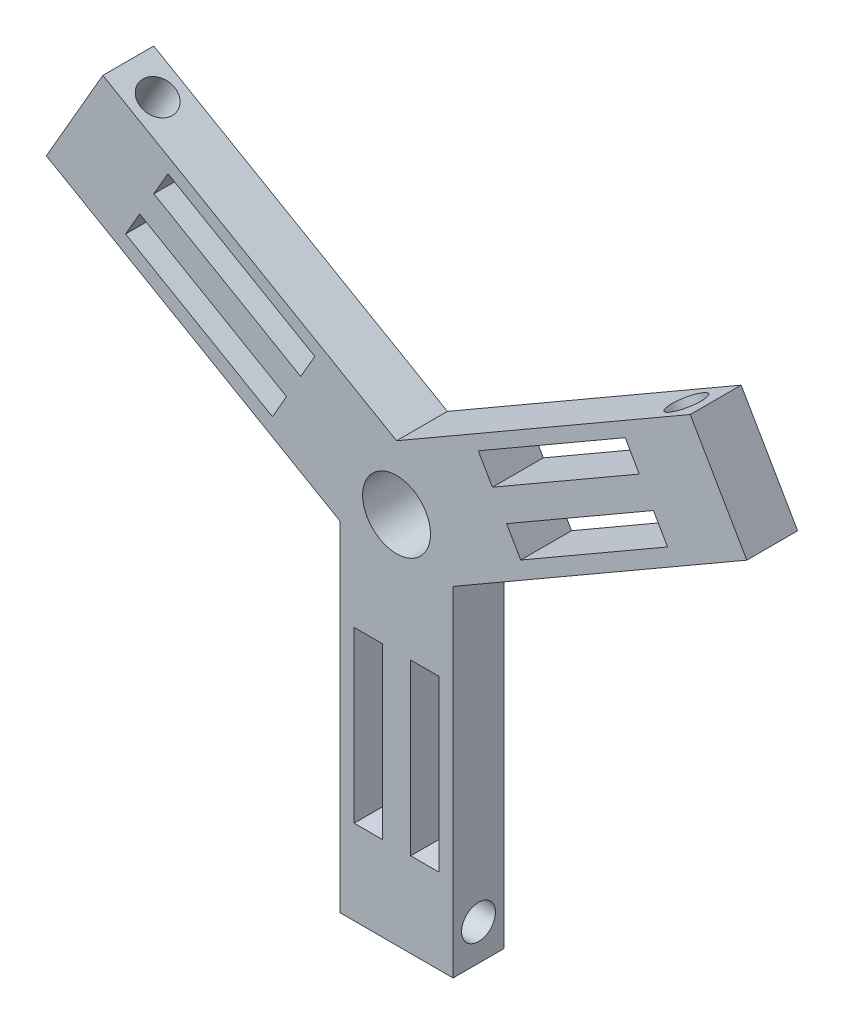
SolidWorks part; units mm, degrees
ref_plane "Front Plane" through (0, 0, 0) normal (0, 0, 1) x (1, 0, 0)
ref_plane "Top Plane" through (0, 0, 0) normal (0, 1, 0) x (1, 0, 0)
ref_plane "Right Plane" through (0, 0, 0) normal (1, 0, 0) x (0, 0, -1)
sketch "Sketch2" plane through (0, 0, 0) normal (0, 0, 1) x (1, 0, 0)
  line L4 (-100, -60) -> (-100, -660)
  line L5 (-100, -660) -> (100, -660)
  line L6 (100, -660) -> (100, -60)
  line L7 (0, 113.2051) -> (519.6152, 413.2051)
  line L8 (519.6152, 413.2051) -> (619.6152, 240)
  line L9 (619.6152, 240) -> (100, -60)
  line L10 (0, 113.2051) -> (-519.6152, 413.2051)
  line L11 (-519.6152, 413.2051) -> (-619.6152, 240)
  line L12 (-619.6152, 240) -> (-100, -60)
  circle A0 centre (0, 0) radius 60
  point P10 (0, 0)
  dimension "D1" = 120
  dimension "D2" = 200
  dimension "D3" = 200
  dimension "D4" = 600
  dimension "D5" = 200
  dimension "D6" = 600
  dimension "D7" = 600
  dimension "D8" = 200
  dimension "D9" = 660
extrude "Boss-Extrude1" add sketch "Sketch2" along normal blind 90
sketch "Sketch4" plane through (0, 0, 90) normal (0, 0, 1) x (1, 0, 0)
  line L0 (0, 0) -> (0, -738.4835) construction
  line L1 (50, -360.3099) -> (50, -363.0394) construction
  line L2 (-25, -510.3099) -> (-75, -510.3099)
  line L3 (49.5451, -363.0394) -> (50.4549, -363.0394) construction
  line L4 (25, -210.3099) -> (75, -210.3099)
  line L5 (25, -210.3099) -> (25, -510.3099)
  line L6 (25, -510.3099) -> (75, -510.3099)
  line L7 (75, -210.3099) -> (75, -510.3099)
  line L8 (25, -210.3099) -> (75, -510.3099) construction
  line L9 (25, -510.3099) -> (75, -210.3099) construction
  line L10 (-75, -210.3099) -> (-75, -510.3099)
  line L11 (-25, -210.3099) -> (-75, -210.3099)
  line L12 (-25, -210.3099) -> (-25, -510.3099)
  point P5 (0, -591.5751)
  point P6 (0, -738.4835)
  point P8 (50, -360.3099)
  dimension "D2" = 300
  dimension "D3" = 50
extrude "Cut-Extrude1" cut sketch "Sketch4" against normal blind 90
pattern_circular "CirPattern1" count 3 every 120 about axis through (0, 0, 0) along (0, 0, 1) of "Cut-Extrude1"
sketch "Sketch7" plane through (-50.9808, -88.3013, 0) normal (-0.5, -0.866, 0) x (0.866, -0.5, 0)
  line L0 (-656.6025, 90) -> (-656.6025, 0) construction
  line L2 (-656.6025, 0) -> (-56.6025, 0) construction
  circle A0 centre (-596.6025, 45) radius 30
  dimension "D1" = 60
  dimension "D2" = 60
  dimension "D3" = 45
extrude "Cut-Extrude2" cut sketch "Sketch7" against normal through all
pattern_circular "CirPattern2" count 3 every 120 about axis through (0, 0, 0) along (0, 0, 1) of "Cut-Extrude2"
